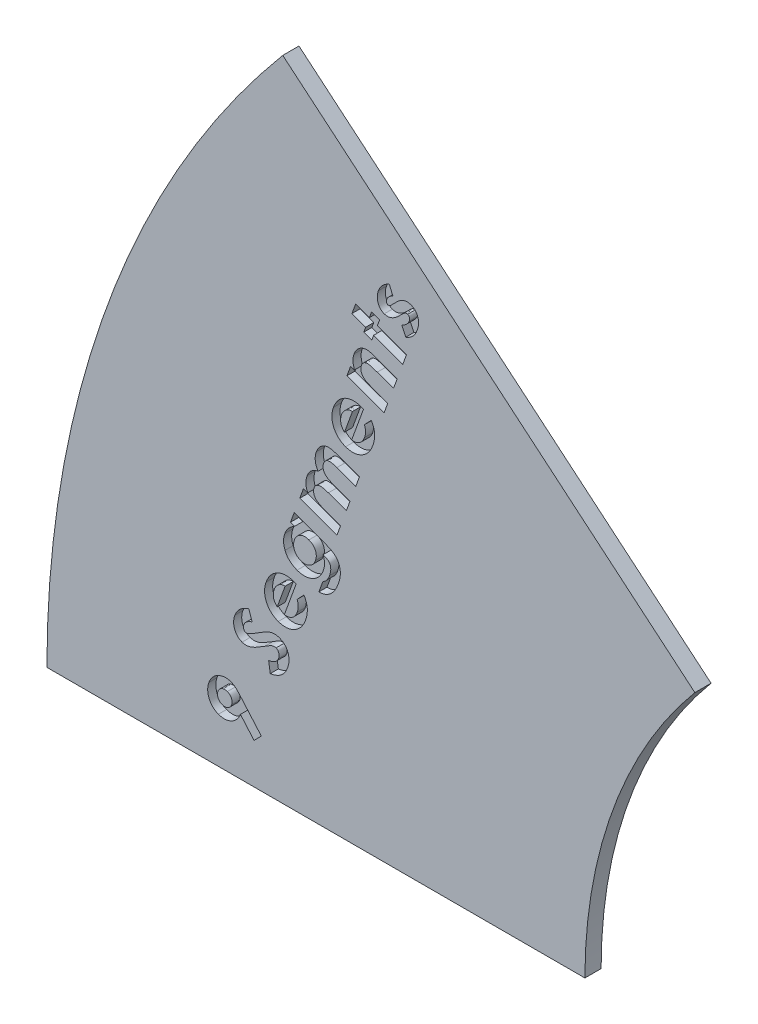
SolidWorks part; units mm, degrees
ref_plane "Front Plane" through (0, 0, 0) normal (0, 0, 1) x (1, 0, 0)
ref_plane "Top Plane" through (0, 0, 0) normal (0, 1, 0) x (1, 0, 0)
ref_plane "Right Plane" through (0, 0, 0) normal (1, 0, 0) x (0, 0, -1)
sketch "Sketch2" plane through (0, 0, 0) normal (0, 0, 1) x (1, 0, 0)
  line L0 (0, 0) -> (105.4453, 0)
  line L1 (127, 59.2211) -> (46.2242, 127)
  arc A0 (0, 0) -> (46.2242, 127) centre (197.5769, 0) cw
  arc A1 (105.4453, 0) -> (127, 59.2211) centre (197.5769, 0) cw
  dimension "D1" = 40
  dimension "D2" = 127
  dimension "D3" = 127
extrude "Boss-Extrude1" add sketch "Sketch2" along normal blind 3.175
sketch "Sketch3" plane through (0, 0, 3.175) normal (0, 0, 1) x (1, 0, 0)
  line L0 (38.3309, 0) -> (75.5874, 102.3614) construction
  line L1 (0, 0) -> (105.4453, 0) construction
  line L2 (127, 59.2211) -> (46.2242, 127) construction
  text T0 "<b>9 Segments</b>" font "Century Gothic" height in points 40
  dimension "D1" = 38.3309
  dimension "D2" = 38.3309
extrude "Cut-Extrude1" cut sketch "Sketch3" against normal blind 1.5875
